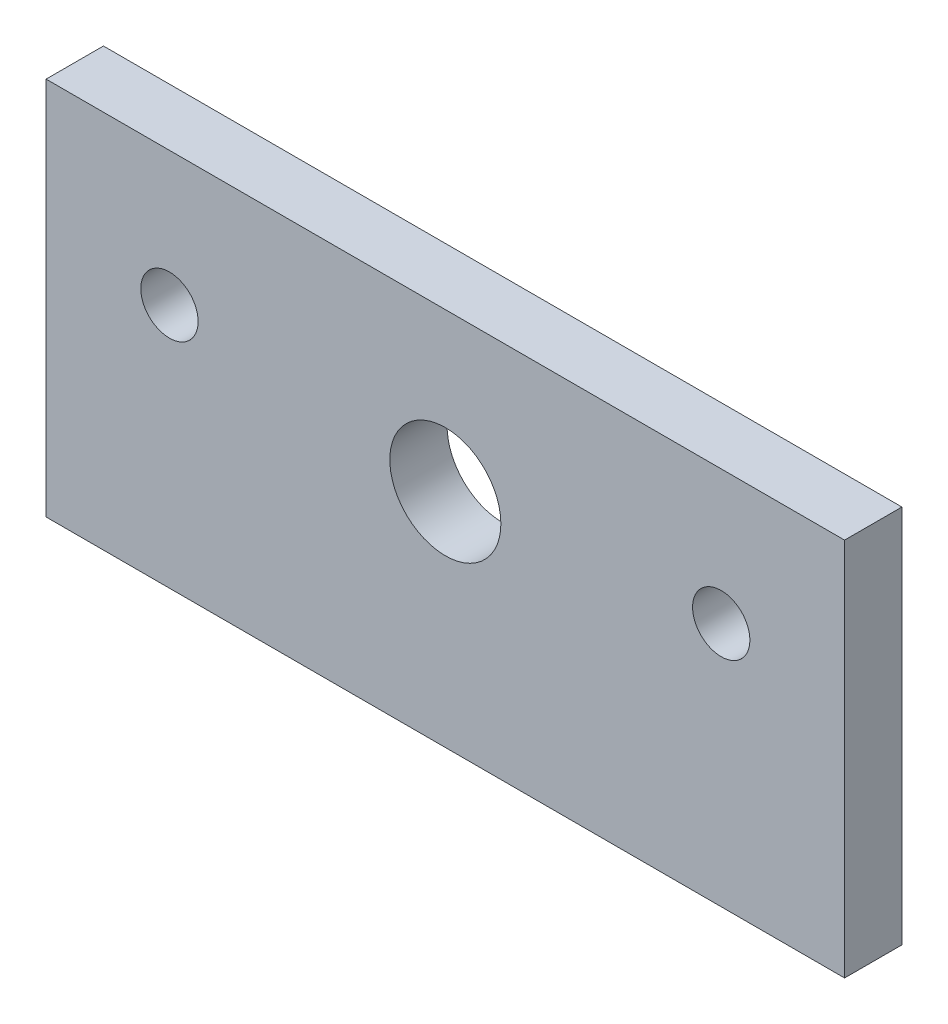
SolidWorks part; units mm, degrees
ref_plane "Front" through (0, 0, 0) normal (0, 0, 1) x (1, 0, 0)
ref_plane "Top" through (0, 0, 0) normal (0, 1, 0) x (1, 0, 0)
ref_plane "Right" through (0, 0, 0) normal (1, 0, 0) x (0, 0, -1)
sketch "Sketch1" plane through (0, 0, 0) normal (0, 0, 1) x (1, 0, 0)
  line L0 (-17.7167, -24.7168) -> (17.2833, -24.7168)
  line L1 (-55.9296, 11.2832) -> (55.4962, 11.2832)
  line L2 (-55.9296, 11.2832) -> (-55.9296, -36.5579)
  line L3 (55.4962, 11.2832) -> (55.4962, -41.6379)
  line L4 (55.4962, -41.6379) -> (-55.9296, -41.6379)
  line L5 (-55.9296, -41.6379) -> (-55.9296, -36.5579)
  circle A0 centre (38.2833, -7.4168) radius 4
  circle A1 centre (-0.2167, -10.7168) radius 5
  circle A2 centre (-38.7167, -7.4168) radius 4
extrude "Boss-Extrude1" add sketch "Sketch1" along normal blind 8
sketch "Sketch2" plane through (0, 0, 8) normal (0, 0, 1) x (1, 0, 0)
  circle A0 centre (-0.2167, -10.7168) radius 7.75
  dimension "D1" = 15.5
extrude "Cut-Extrude1" cut sketch "Sketch2" against normal through all
sketch "Sketch3" plane through (0, 0, 0) normal (0, 0, 1) x (1, 0, 0)
  line L0 (55.4962, -41.6379) -> (-55.9296, -41.6379) construction
  line L1 (55.4962, 11.2832) -> (55.4962, -41.6379) construction
  line L2 (-55.9296, -41.6379) -> (-55.9296, 11.2832) construction
  line L3 (-55.9296, 11.2832) -> (55.4962, 11.2832) construction
  line L4 (55.4962, -41.6379) -> (-55.9296, -41.6379)
  line L5 (55.4962, 11.2832) -> (55.4962, -41.6379)
  line L6 (-55.9296, -41.6379) -> (-55.9296, 11.2832)
  line L7 (-55.9296, 11.2832) -> (55.4962, 11.2832)
  circle A0 centre (38.2833, -7.4168) radius 4 construction
  circle A1 centre (-38.7167, -7.4168) radius 4 construction
  circle A2 centre (-0.2167, -10.7168) radius 7.75 construction
  circle A3 centre (38.2833, -7.4168) radius 4
  circle A4 centre (-38.7167, -7.4168) radius 4
  circle A5 centre (-0.2167, -10.7168) radius 7.75
